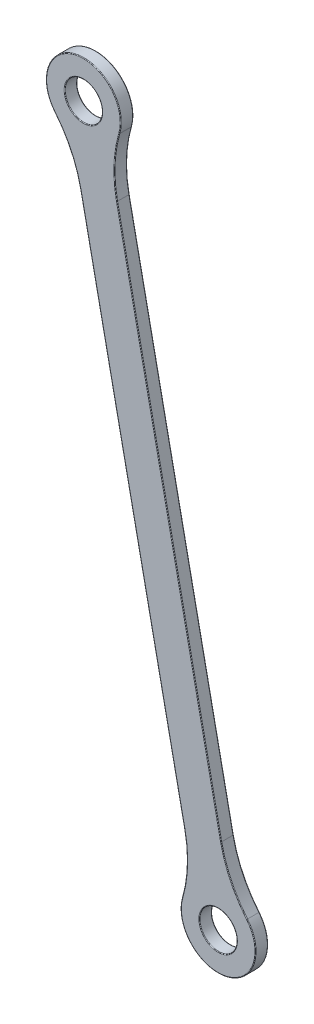
SolidWorks part; units mm, degrees
ref_plane "Płaszczyzna przednia" through (0, 0, 0) normal (0, 0, 1) x (1, 0, 0)
ref_plane "Płaszczyzna górna" through (0, 0, 0) normal (0, 1, 0) x (1, 0, 0)
ref_plane "Płaszczyzna prawa" through (0, 0, 0) normal (1, 0, 0) x (0, 0, -1)
sketch "Szkic1" plane through (0, 0, 0) normal (0, 0, 1) x (1, 0, 0)
  line L0 (33.78, 49.7571) -> (1.3329, 206.4325) construction
  line L1 (33.78, 49.7571) -> (1.3329, 206.4325) construction
sketch "Szkic2" plane through (0, 0, 0) normal (0, 0, 1) x (1, 0, 0)
  line L0 (33.78, 49.7571) -> (1.3329, 206.4325) construction
  line L1 (33.78, 49.7571) -> (1.3329, 206.4325) construction
  line L2 (29.3735, 48.8445) -> (-3.0736, 205.5199)
  line L3 (38.1865, 50.6697) -> (5.7394, 207.3451)
  circle A0 centre (1.3329, 206.4325) radius 9
  circle A1 centre (33.78, 49.7571) radius 9
  arc A2 (29.3735, 48.8445) -> (38.1865, 50.6697) centre (33.78, 49.7571) ccw
  arc A3 (5.7394, 207.3451) -> (-3.0736, 205.5199) centre (1.3329, 206.4325) ccw
  arc A4 (-3.0736, 205.5199) -> (5.7394, 207.3451) centre (1.3329, 206.4325) ccw
  arc A5 (29.3735, 48.8445) -> (38.1865, 50.6697) centre (33.78, 49.7571) cw
  point P7 (17.5565, 128.0948)
  dimension "D1" = 18
  dimension "D2" = 9
extrude "Dodanie-wyciągnięcie1" add sketch "Szkic2" along normal blind 3 contours A3 L3 A0 L2 | A1 L0 A0 L2 | L0 A1 L3 A0 | A2 L2 A1 L3 | A5 L0 A1 L2 | L0 A5 L3 A1 | A0 L0 A4 L2 | L0 A0 L3 A4
fillet "Zaokrąglenie1" radius 30 1 edges at (-1.4929, 197.8877, 1.5)
fillet "Zaokrąglenie2" radius 30 1 edges at (7.3201, 199.7128, 1.5)
fillet "Zaokrąglenie3" radius 30 1 edges at (27.7929, 56.4768, 1.5)
fillet "Zaokrąglenie4" radius 30 1 edges at (36.6059, 58.3019, 1.5)
fillet "Zaokrąglenie5" radius 0.15 20 edges at (38.28, 49.7571, 3) (38.28, 49.7571, 0) (5.8329, 206.4325, 3) (5.8329, 206.4325, 0) (36.8197, 61.6004, 3) (36.8197, 61.6004, 0) (21.963, 129.0074, 3) (21.963, 129.0074, 0) (8.8263, 196.7706, 3) (8.8263, 196.7706, 0) (-0.4922, 215.2455, 3) (-0.4922, 215.2455, 0) (-1.7067, 194.5892, 3) (-1.7067, 194.5892, 0) (13.15, 127.1822, 0) (13.15, 127.1822, 3) (26.2867, 59.419, 3) (26.2867, 59.419, 0) (35.6051, 40.9441, 0) (35.6051, 40.9441, 3)
